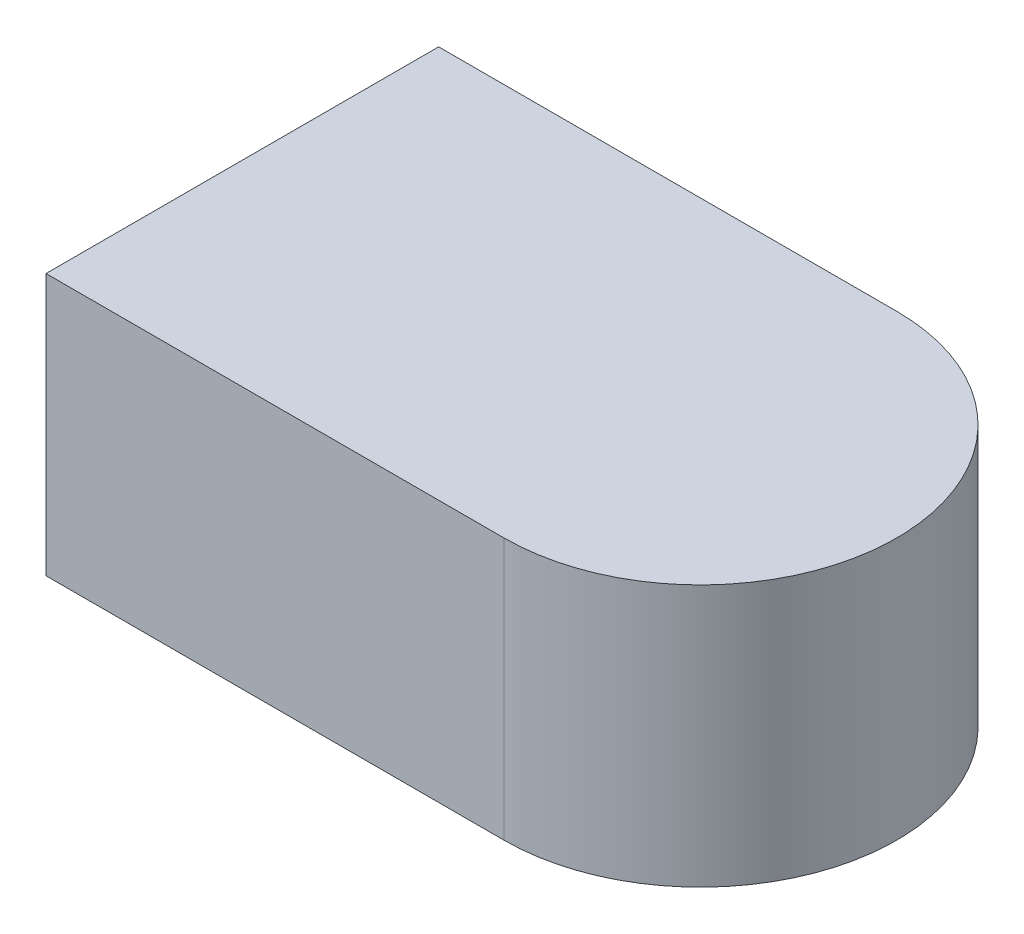
SolidWorks part; units mm, degrees
ref_plane "Front Plane" through (0, 0, 0) normal (0, 0, 1) x (1, 0, 0)
ref_plane "Top Plane" through (0, 0, 0) normal (0, 1, 0) x (1, 0, 0)
ref_plane "Right Plane" through (0, 0, 0) normal (1, 0, 0) x (0, 0, -1)
sketch "Sketch1" plane through (0, 0, 0) normal (0, 1, 0) x (1, 0, 0)
  line L1 (-0.175, -0.15) -> (0.175, -0.15)
  line L2 (-0.175, -0.15) -> (-0.175, 0.15)
  line L3 (-0.175, 0.15) -> (0.175, 0.15)
  line L5 (-0.175, -0.15) -> (0.175, 0.15) construction
  line L6 (-0.175, 0.15) -> (0.175, -0.15) construction
  arc A0 (0.175, 0.15) -> (0.175, -0.15) centre (0.175, 0) cw
  point P0 (0, 0)
  point P7 (0.325, 0)
  dimension "D1" = 0.3
  dimension "D2" = 0.5
extrude "Boss-Extrude1" add sketch "Sketch1" along normal blind 0.2
